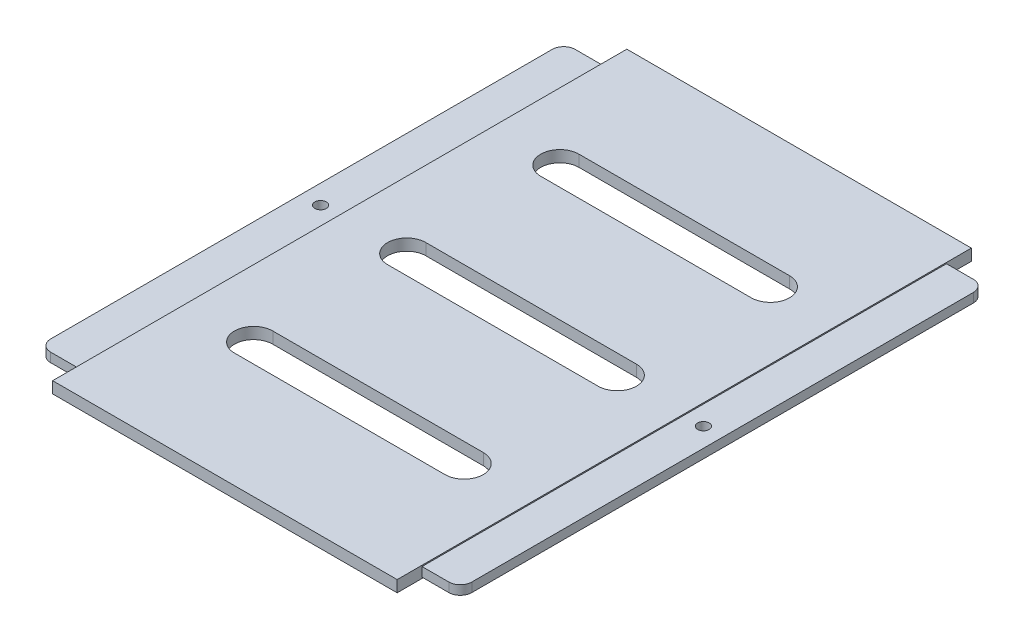
SolidWorks part; units mm, degrees
ref_plane "前视基准面" through (0, 0, 0) normal (0, 0, 1) x (1, 0, 0)
ref_plane "上视基准面" through (0, 0, 0) normal (0, 1, 0) x (1, 0, 0)
ref_plane "右视基准面" through (0, 0, 0) normal (1, 0, 0) x (0, 0, -1)
other "Configuration Table"
sketch "草图1" plane through (0, 0, 0) normal (0, 1, 0) x (1, 0, 0)
  line L1 (-45, 75) -> (45, 75)
  line L2 (-45, 75) -> (-45, -75)
  line L3 (-45, -75) -> (45, -75)
  line L4 (45, 75) -> (45, -75)
  line L5 (-45, 75) -> (45, -75) construction
  line L6 (-45, -75) -> (45, 75) construction
  point P0 (0, 0)
  dimension "D1" = 90
  dimension "D2" = 150
extrude "凸台-拉伸1" add sketch "草图1" along normal blind 3
sketch "草图2" plane through (0, 3, 0) normal (0, 1, 0) x (1, 0, 0)
  line L0 (-45, 0) -> (45, 0)
  line L1 (-45, 75) -> (-45, -75) construction
  line L2 (45, -75) -> (45, 75) construction
  line L3 (0, 71.0556) -> (0, -75)
  line L4 (-45, -75) -> (45, -75) construction
  line L5 (-45, 40) -> (45, 40)
  line L6 (-45, -40) -> (45, -40)
  line L7 (-27.5, 40) -> (27.5, 40) construction
  line L8 (-27.5, 45) -> (27.5, 45)
  line L9 (-27.5, 35) -> (27.5, 35)
  line L10 (-27.5, 0) -> (27.5, 0) construction
  line L11 (-27.5, 5) -> (27.5, 5)
  line L12 (-27.5, -5) -> (27.5, -5)
  line L13 (-27.5, -40) -> (27.5, -40) construction
  line L14 (-27.5, -35) -> (27.5, -35)
  line L15 (-27.5, -45) -> (27.5, -45)
  arc A0 (-27.5, 45) -> (-27.5, 35) centre (-27.5, 40) ccw
  arc A1 (27.5, 35) -> (27.5, 45) centre (27.5, 40) ccw
  arc A2 (-27.5, 5) -> (-27.5, -5) centre (-27.5, 0) ccw
  arc A3 (27.5, -5) -> (27.5, 5) centre (27.5, 0) ccw
  arc A4 (-27.5, -35) -> (-27.5, -45) centre (-27.5, -40) ccw
  arc A5 (27.5, -45) -> (27.5, -35) centre (27.5, -40) ccw
  point P16 (0, 40)
  point P22 (0, 0)
  point P30 (0, -40)
  dimension "D6" = 5
  dimension "D7" = 5
  dimension "D8" = 5
  dimension "D1" = 40
  dimension "D2" = 40
  dimension "D3" = 55
  dimension "D4" = 55
  dimension "D5" = 55
  dimension "D9" = 40
extrude "切除-拉伸1" cut sketch "草图2" against normal blind 3 contours L8 A0 L5 L3 | L5 A1 L8 L3 | L5 A0 L9 L3 | L9 A1 L5 L3 | L11 A2 L0 L3 | L0 A3 L11 L3 | L12 A3 L0 L3 | L0 A2 L12 L3 | L14 A4 L6 L3 | L6 A5 L14 L3 | L6 A4 L15 L3 | L15 A5 L6 L3
sketch "草图4" plane through (45, 0, 0) normal (1, 0, 0) x (0, 0, -1)
  line L0 (-75, 1.5) -> (74.0476, 1.5)
  line L1 (-75, 3) -> (-75, 0) construction
  line L3 (-68.5, 2.7) -> (68.5, 2.7)
  line L4 (-68.5, 2.7) -> (-68.5, 0.3)
  line L5 (-68.5, 0.3) -> (68.5, 0.3)
  line L6 (68.5, 2.7) -> (68.5, 0.3)
  line L7 (-68.5, 2.7) -> (68.5, 0.3) construction
  line L8 (-68.5, 0.3) -> (68.5, 2.7) construction
  point P4 (0, 1.5)
  dimension "D1" = 137
  dimension "D2" = 2.4
extrude "凸台-拉伸2" add sketch "草图4" along normal blind 10 contours L6 L0 L4 L5 | L6 L3 L4 L0
sketch "草图5" plane through (-45, 0, 0) normal (-1, 0, 0) x (0, 0, 1)
  line L0 (-75, 1.5) -> (75, 1.5)
  line L1 (-75, 3) -> (-75, 0) construction
  line L2 (75, 3) -> (75, 0) construction
  line L4 (-68.5, 2.7) -> (68.5, 2.7)
  line L5 (-68.5, 2.7) -> (-68.5, 0.3)
  line L6 (-68.5, 0.3) -> (68.5, 0.3)
  line L7 (68.5, 2.7) -> (68.5, 0.3)
  line L8 (-68.5, 2.7) -> (68.5, 0.3) construction
  line L9 (-68.5, 0.3) -> (68.5, 2.7) construction
  point P6 (0, 1.5)
  dimension "D1" = 137
  dimension "D2" = 2.4
extrude "凸台-拉伸3" add sketch "草图5" along normal blind 10 contours L7 L4 L5 L0 | L7 L0 L5 L6
fillet "圆角1" radius 3 4 edges at (55, 1.5, -68.5) (55, 1.5, 68.5) (-55, 1.5, 68.5) (-55, 1.5, -68.5)
sketch "草图6" plane through (0, 2.7, 0) normal (0, 1, 0) x (1, 0, 0)
  line L0 (55, 65.5) -> (45, 65.5) construction
  line L1 (45, -68.5) -> (45, 68.5) construction
  line L2 (50, 65.5) -> (50, -68.5) construction
  line L3 (52, -68.5) -> (45, -68.5) construction
  line L4 (45, 0) -> (55, 0) construction
  line L5 (55, -65.5) -> (55, 65.5) construction
  circle A0 centre (50, 0) radius 1.5
  point P14 (50, 0)
  dimension "D1" = 3
extrude "切除-拉伸2" cut sketch "草图6" against normal blind 10
sketch "草图7" plane through (0, 2.7, 0) normal (0, 1, 0) x (1, 0, 0)
  line L0 (-55, 65.5) -> (-45, 65.5) construction
  line L1 (-45, 68.5) -> (-45, -68.5) construction
  line L2 (-50, 65.5) -> (-50, -68.5) construction
  line L3 (-52, -68.5) -> (-45, -68.5) construction
  line L4 (-45, 0) -> (-55, 0) construction
  line L5 (-55, 65.5) -> (-55, -65.5) construction
  circle A0 centre (-50, 0) radius 1.5
  point P14 (-50, 0)
  dimension "D1" = 3
extrude "切除-拉伸3" cut sketch "草图7" against normal blind 10
